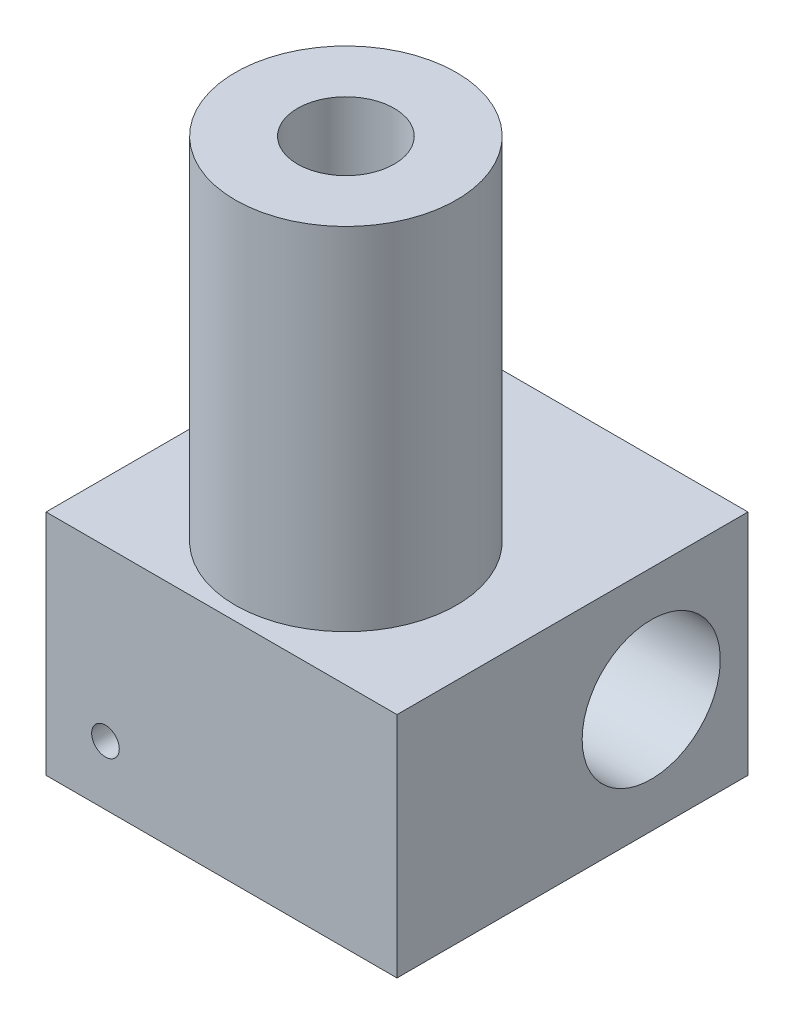
SolidWorks part; units mm, degrees
ref_plane "Front Plane" through (0, 0, 0) normal (0, 0, 1) x (1, 0, 0)
ref_plane "Top Plane" through (0, 0, 0) normal (0, 1, 0) x (1, 0, 0)
ref_plane "Right Plane" through (0, 0, 0) normal (1, 0, 0) x (0, 0, -1)
sketch "Sketch1" plane through (0, 0, 0) normal (0, 1, 0) x (1, 0, 0)
  line L1 (-6.35, 6.35) -> (6.35, 6.35)
  line L2 (-6.35, 6.35) -> (-6.35, -6.35)
  line L3 (-6.35, -6.35) -> (6.35, -6.35)
  line L4 (6.35, 6.35) -> (6.35, -6.35)
extrude "Extrude1" add sketch "Sketch1" along normal blind 8.255
sketch "Sketch2" plane through (0, 8.255, 0) normal (0, 1, 0) x (1, 0, 0)
  circle A0 centre (0, -1.85) radius 4
extrude "Extrude2" add sketch "Sketch2" along normal blind 12.7
sketch "Sketch3" plane through (0, 20.955, 0) normal (0, 1, 0) x (-1, 0, 0)
  circle A0 centre (0, 1.85) radius 1.75
sketch "Sketch4" plane through (0, 0, 0) normal (0, -1, 0) x (1, 0, 0)
  line L0 (0, 6.35) -> (0, 1.85)
  line L1 (-6.35, 6.35) -> (6.35, 6.35) construction
  circle A0 centre (0, 1.85) radius 4
extrude "Extrude8" add sketch "Sketch4" along normal blind 2.5 draft 51
sketch "Sketch5" plane through (0, -2.5, 0) normal (0, -1, 0) x (1, 0, 0)
  circle A0 centre (0, 1.85) radius 0.25
extrude "Extrude9" cut sketch "Sketch5" against normal blind 2.5
extrude "Extrude10" cut sketch "Sketch3" against normal blind 20.955
sketch "Sketch7" plane through (-6.35, 0, 0) normal (-1, 0, 0) x (0, 0, 1)
  circle A0 centre (-2.85, 4.1275) radius 2.5
extrude "Extrude11" cut sketch "Sketch7" against normal up to surface (12.7 mm away) up to face at (6.35, 4.1275, 0)
sketch "Sketch8" plane through (0, 0, 6.35) normal (0, 0, 1) x (1, 0, 0)
  circle A0 centre (-4.1999, 2.1501) radius 0.5
extrude "Extrude12" cut sketch "Sketch8" against normal blind 2.5
